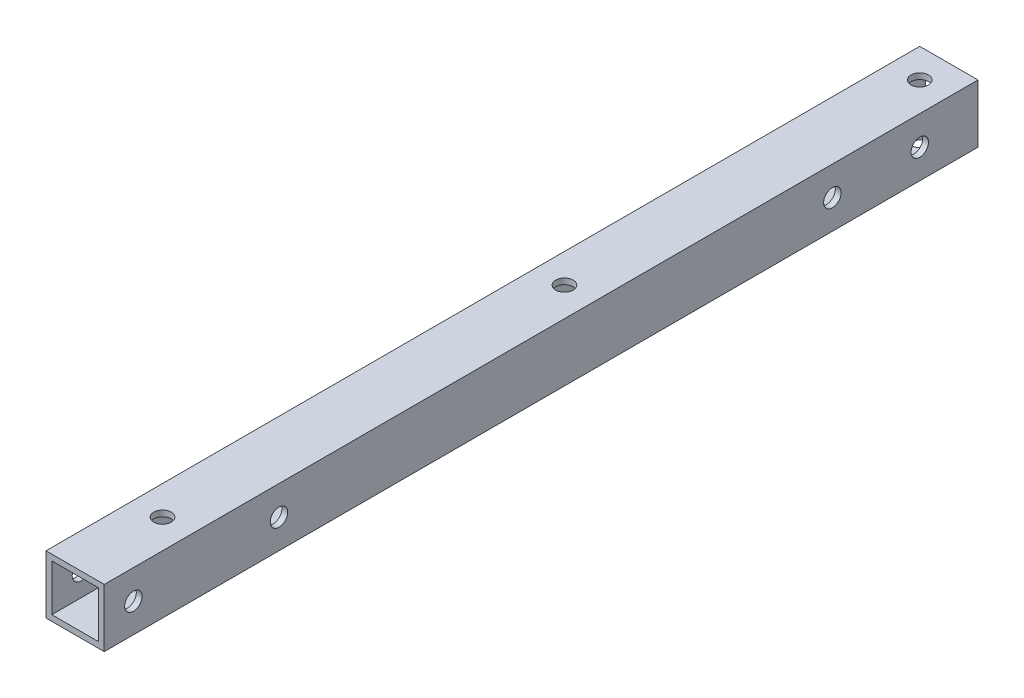
SolidWorks part; units mm, degrees
material "6063-O"
ref_plane "前视基准面" through (0, 0, 0) normal (0, 0, 1) x (1, 0, 0)
ref_plane "上视基准面" through (0, 0, 0) normal (0, 1, 0) x (1, 0, 0)
ref_plane "右视基准面" through (0, 0, 0) normal (1, 0, 0) x (0, 0, -1)
other "Configuration Table"
sketch "草图1" plane through (0, 0, 0) normal (0, 0, 1) x (1, 0, 0)
  line L1 (9.1611, -154.1127) -> (-0.8389, -154.1127)
  line L2 (9.1611, -154.1127) -> (9.1611, -164.1127)
  line L3 (9.1611, -164.1127) -> (-0.8389, -164.1127)
  line L4 (-0.8389, -154.1127) -> (-0.8389, -164.1127)
  line L5 (9.1611, -154.1127) -> (-0.8389, -164.1127) construction
  line L6 (9.1611, -164.1127) -> (-0.8389, -154.1127) construction
  point P4 (4.1611, -159.1127)
  dimension "D1" = 10
  dimension "D2" = 10
extrude "拉伸-薄壁1" add sketch "草图1" along normal blind 150 thin thin type one direction reverse wall 1
sketch "草图2" plane through (0, -164.1127, 0) normal (0, -1, 0) x (1, 0, 0)
  line L0 (4.1611, 150) -> (4.1611, 0) construction
  line L1 (-0.8389, 150) -> (9.1611, 150) construction
  line L2 (-0.8389, 0) -> (9.1611, 0) construction
  circle A2 centre (4.1611, 135) radius 1.5
  circle A3 centre (4.1611, 66) radius 1.5
  circle A4 centre (4.1611, 5) radius 1.5
  dimension "D1" = 3
  dimension "D2" = 5
  dimension "D3" = 61
  dimension "D4" = 15
extrude "切除-拉伸1" cut sketch "草图2" against normal through all
sketch "草图3" plane through (9.1611, 0, 0) normal (1, 0, 0) x (0, 0, -1)
  line L0 (0, -159.1127) -> (-150, -159.1127) construction
  line L1 (0, -164.1127) -> (0, -154.1127) construction
  line L4 (-150, -164.1127) -> (-150, -154.1127) construction
  line L6 (-150, -154.1127) -> (-140, -164.1127) construction
  line L7 (-150, -164.1127) -> (0, -164.1127) construction
  line L8 (-140, -164.1127) -> (-150, -164.1127) construction
  line L9 (-150, -164.1127) -> (-150, -154.1127) construction
  circle A0 centre (-25, -159.1127) radius 1.5
  circle A1 centre (-10, -159.1127) radius 1.5
  circle A2 centre (-120, -159.1127) radius 1.5
  circle A3 centre (-135, -159.1127) radius 1.5 construction
  circle A4 centre (-155, -159.1127) radius 1.5 construction
  circle A5 centre (-145, -159.1127) radius 1.5
  dimension "D1" = 3
  dimension "D2" = 10
  dimension "D3" = 15
  dimension "D4" = 145
  dimension "D5" = 15
  dimension "D7" = 10
  dimension "D8" = 10
  dimension "D6" = 45
extrude "切除-拉伸2" cut sketch "草图3" against normal through all
